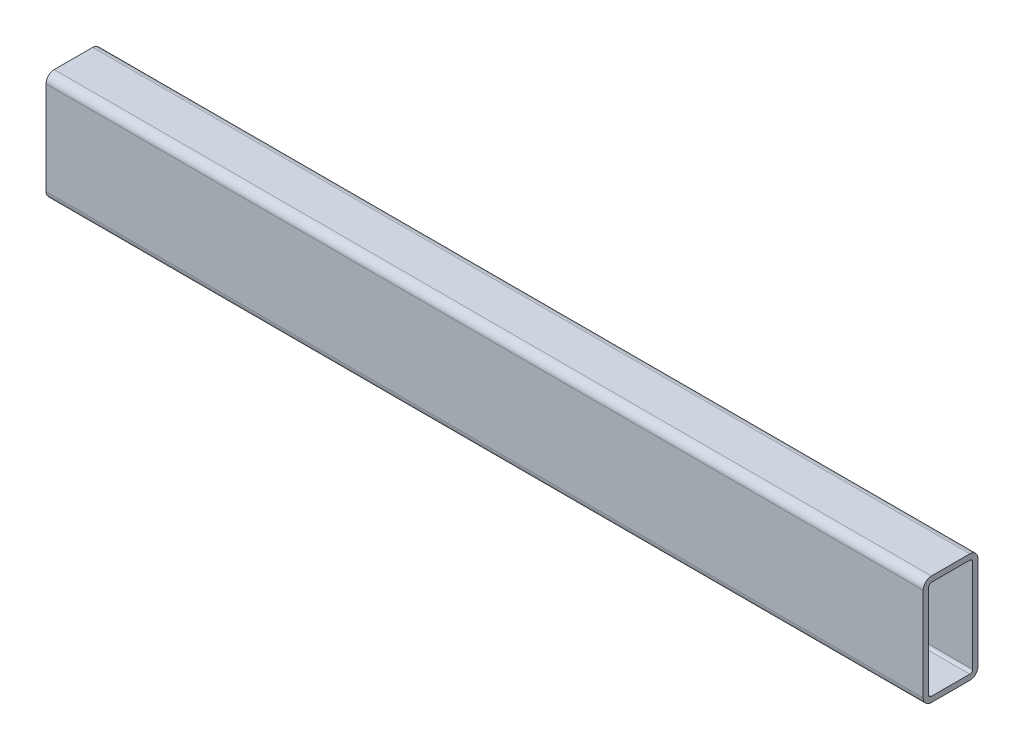
SolidWorks part; units mm, degrees
ref_plane "Спереди" through (0, 0, 0) normal (0, 0, 1) x (1, 0, 0)
ref_plane "Сверху" through (0, 0, 0) normal (0, 1, 0) x (1, 0, 0)
ref_plane "Справа" through (0, 0, 0) normal (1, 0, 0) x (0, 0, -1)
sketch "Эскиз1" plane through (0, 0, 0) normal (1, 0, 0) x (0, 0, -1)
  line L1 (1, 0) -> (15, 0)
  line L2 (0, 1) -> (0, 35)
  line L3 (1, 36) -> (15, 36)
  line L4 (16, 1) -> (16, 35)
  arc A4 (1, 0) -> (0, 1) centre (1, 1) cw
  arc A5 (15, 0) -> (16, 1) centre (15, 1) ccw
  arc A6 (16, 35) -> (15, 36) centre (15, 35) ccw
  arc A7 (0, 35) -> (1, 36) centre (1, 35) cw
  point P0 (0, 37.6724)
  point P3 (0, 0)
  point P5 (0, 0)
  point P8 (0, 0)
  dimension "D1" = 1
extrude "Вытянуть-Тонкостенный1" add sketch "Эскиз1" along normal blind 320 thin
